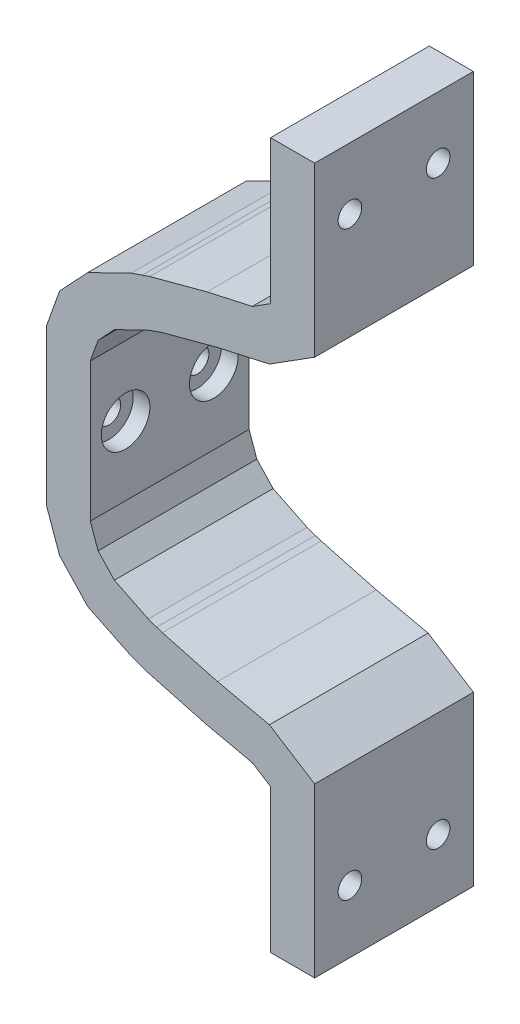
SolidWorks part; units mm, degrees
ref_plane "Front Plane" through (0, 0, 0) normal (0, 0, 1) x (1, 0, 0)
ref_plane "Top Plane" through (0, 0, 0) normal (0, 1, 0) x (1, 0, 0)
ref_plane "Right Plane" through (0, 0, 0) normal (1, 0, 0) x (0, 0, -1)
sketch "Model" plane through (0, 0, 0) normal (0, 0, 1) x (1, 0, 0)
  line L0 (-31.5615, 5.719) -> (-31.5592, -16.7565)
  line L35 (-15.7136, 12.9115) -> (-14.8809, 13.188)
  line L36 (-14.8809, 13.188) -> (-6.9454, 15.3129)
  line L37 (-6.9454, 15.3129) -> (0.5162, 16.9685)
  line L38 (0.5162, 16.9685) -> (7.0365, 21.0824)
  line L53 (0.5162, -28.0048) -> (7.0365, -32.1186)
  line L54 (-6.9454, -26.3491) -> (0.5162, -28.0048)
  line L55 (-14.8809, -24.2242) -> (-6.9454, -26.3491)
  line L56 (-15.7136, -23.9477) -> (-14.8809, -24.2242)
  line L57 (-16.9096, -23.527) -> (-15.7136, -23.9477)
  line L58 (-21.8042, -21.1418) -> (-16.9096, -23.527)
  line L59 (-24.1425, -18.6446) -> (-21.8042, -21.1418)
  line L60 (-25.2646, -15.5017) -> (-24.1425, -18.6446)
  line L65 (-25.2667, 4.4655) -> (-24.1471, 7.6035)
  line L66 (-24.1471, 7.6035) -> (-21.8042, 10.1055)
  line L67 (-21.8042, 10.1055) -> (-16.9096, 12.4907)
  line L68 (-16.9096, 12.4907) -> (-15.7136, 12.9115)
  line L71 (0.6865, -35.6205) -> (0.6865, -56.3181)
  line L72 (-17.768, 18.9202) -> (-16.7043, 19.2734)
  line L73 (-16.7043, 19.2734) -> (-8.4551, 21.4823)
  line L74 (-8.4551, 21.4823) -> (-1.9379, 22.9284)
  line L75 (-1.9379, 22.9284) -> (0.6865, 24.5842)
  line L77 (52.7242, -5.5181) -> (1077.4342, -5.5181) construction
  line L78 (-1.9379, -33.9647) -> (0.6865, -35.6205)
  line L79 (-8.4551, -32.5186) -> (-1.9379, -33.9647)
  line L80 (-16.7043, -30.3097) -> (-8.4551, -32.5186)
  line L81 (-17.768, -29.9565) -> (-16.7043, -30.3097)
  line L82 (-19.3623, -29.3956) -> (-17.768, -29.9565)
  line L83 (-25.6388, -26.337) -> (-19.3623, -29.3956)
  line L84 (-29.6793, -22.0221) -> (-25.6388, -26.337)
  line L85 (-31.5592, -16.7565) -> (-29.6793, -22.0221)
  line L90 (-31.5615, 5.719) -> (-29.6843, 10.9804)
  line L91 (-29.6843, 10.9804) -> (-25.6388, 15.3007)
  line L92 (-25.6388, 15.3007) -> (-19.3623, 18.3593)
  line L93 (-19.3623, 18.3593) -> (-17.768, 18.9202)
  line L95 (7.0365, 45.2819) -> (0.6865, 45.2819)
  line L106 (7.0365, -56.3181) -> (0.6865, -56.3181)
  line L107 (0.6865, 45.2819) -> (0.6865, 24.5842)
  line L108 (7.0365, 21.0824) -> (7.0365, 45.2819)
  line L109 (7.0365, -32.1186) -> (7.0365, -56.3181)
  line L111 (-25.2667, 4.4655) -> (-25.2646, -15.5017)
  dimension "D1" = 0.5162
  dimension "D2" = 0.6865
  dimension "D3" = 7.0365
  dimension "D4" = 1.9379
  dimension "D5" = 6.9454
  dimension "D6" = 8.4551
  dimension "D7" = 14.8809
  dimension "D8" = 15.7136
  dimension "D9" = 16.7043
  dimension "D10" = 16.9096
  dimension "D11" = 17.768
  dimension "D12" = 19.3623
  dimension "D13" = 21.8042
  dimension "D14" = 24.1425
  dimension "D15" = 24.1471
  dimension "D16" = 25.2646
  dimension "D17" = 25.2667
  dimension "D18" = 25.6388
  dimension "D19" = 29.6793
  dimension "D20" = 29.6843
  dimension "D21" = 31.5592
  dimension "D22" = 31.5615
  dimension "D24" = 4.4655
  dimension "D25" = 5.719
  dimension "D26" = 7.6035
  dimension "D27" = 10.1055
  dimension "D28" = 10.9804
  dimension "D29" = 12.4907
  dimension "D30" = 12.9115
  dimension "D31" = 13.188
  dimension "D32" = 15.3007
  dimension "D33" = 15.3129
  dimension "D34" = 16.9685
  dimension "D35" = 18.3593
  dimension "D36" = 18.9202
  dimension "D37" = 19.2734
  dimension "D38" = 21.0824
  dimension "D39" = 21.4823
  dimension "D40" = 22.9284
  dimension "D41" = 24.5842
  dimension "D42" = 45.2819
  dimension "D45" = 15.5017
  dimension "D46" = 16.7565
  dimension "D47" = 18.6446
  dimension "D48" = 21.1418
  dimension "D49" = 22.0221
extrude "Boss-Extrude1" add sketch "Model" along normal blind 22.86 contours L74 L75 L107 L95 L108 L38 L37 L36 L35 L68 L67 L66 L65 L111 L60 L59 L58 L57 L56 L55 L54 L53 L109 L106 L71 L78 L79 L80 L81 L82 L83 L84 L85 L0 L90 L91 L92 L93 L72 L73
hole_wizard "M3 Clearance Hole1" positions "Sketch1" profile "Sketch2" hole size "M3" standard "ANSI Metric" end condition through all
sketch "Sketch1" plane through (0.6865, 0, 0) normal (-1, 0, 0) x (0, 0, 1)
  line L0 (0, 45.2819) -> (0, 24.5842) construction
  line L1 (22.86, 45.2819) -> (0, 45.2819) construction
  line L2 (0, -35.6205) -> (0, -56.3181) construction
  line L4 (22.86, -56.3181) -> (0, -56.3181) construction
  point P0 (5.08, 36.3919)
  point P2 (17.78, 36.3919)
  point P4 (5.08, -47.3087)
  point P6 (17.78, -47.3087)
  point P29 (0, 0)
  dimension "D1" = 12.7
  dimension "D2" = 5.08
  dimension "D3" = 8.89
  dimension "D4" = 8.89
  dimension "D5" = 12.7
  dimension "D6" = 5.08
  dimension "D7" = 9.0094
  dimension "D8" = 9.0094
sketch "Sketch2" plane through (0.6865, 36.3919, 5.08) normal (0, 1, 0) x (0, 0, 1)
  line L0 (0, 0) -> (0, 6.35)
  line L1 (0, 6.35) -> (1.7, 6.35)
  line L2 (1.7, 6.35) -> (1.7, 0)
  line L5 (1.7, 0) -> (0, 0)
  line L11 (0, -6.35) -> (0, 107.95) construction
  dimension "Thru Hole Dia." = 3.4
  dimension "Thru Hole Depth" = 6.35
hole_wizard "CBORE for M3 Pan Head Machine Screw1" positions "Sketch3" profile "Sketch4" counterbore size "M3" standard "ANSI Metric" end condition through all
sketch "Sketch3" plane through (-25.2662, -0.0026, 0) normal (1, 0.0001, 0) x (0, 0, -1)
  line L0 (-22.86, 4.4682) -> (-22.86, -15.4991) construction
  line L1 (-22.86, 4.4682) -> (0, 4.4682) construction
  point P0 (-5.08, -5.5648)
  point P2 (-17.78, -5.5648)
  dimension "D1" = 5.08
  dimension "D2" = 12.7
  dimension "D3" = 10.033
sketch "Sketch4" plane through (-25.2656, -5.5675, 5.08) normal (0, 0, 1) x (-0.0001, 1, 0)
  line L0 (0, 0) -> (0, 6.3012)
  line L1 (0, 6.3012) -> (1.7, 6.3012)
  line L3 (1.7, 6.3012) -> (1.7, 2.4)
  line L4 (1.7, 2.4) -> (3.5, 2.4)
  line L5 (3.5, 2.4) -> (3.5, 0)
  line L7 (3.5, 0) -> (0, 0)
  line L11 (0, -6.35) -> (0, 107.95) construction
  dimension "Thru Hole Dia." = 3.4
  dimension "Thru Hole Depth" = 6.3012
  dimension "C'Bore Dia." = 7
  dimension "C'Bore Depth" = 2.4
sketch "Sketch5" plane through (0.6865, 0, 0) normal (-1, 0, 0) x (0, 0, 1)
  line L0 (0, -35.6205) -> (0, -56.3181) construction
  line L1 (17.78, -43.6426) -> (14.605, -45.4756)
  line L2 (14.605, -45.4756) -> (14.605, -49.1418)
  line L3 (14.605, -49.1418) -> (17.78, -50.9749)
  line L4 (17.78, -50.9749) -> (20.955, -49.1418)
  line L5 (20.955, -49.1418) -> (20.955, -45.4756)
  line L6 (20.955, -45.4756) -> (17.78, -43.6426)
  line L7 (5.08, -43.6426) -> (1.905, -45.4756)
  line L8 (1.905, -45.4756) -> (1.905, -49.1418)
  line L9 (1.905, -49.1418) -> (5.08, -50.9749)
  line L10 (5.08, -50.9749) -> (8.255, -49.1418)
  line L11 (8.255, -49.1418) -> (8.255, -45.4756)
  line L12 (8.255, -45.4756) -> (5.08, -43.6426)
  line L13 (17.78, 40.058) -> (14.605, 38.225)
  line L14 (14.605, 38.225) -> (14.605, 34.5588)
  line L15 (14.605, 34.5588) -> (17.78, 32.7257)
  line L16 (17.78, 32.7257) -> (20.955, 34.5588)
  line L17 (20.955, 34.5588) -> (20.955, 38.225)
  line L18 (20.955, 38.225) -> (17.78, 40.058)
  line L19 (5.08, 40.058) -> (1.905, 38.225)
  line L20 (1.905, 38.225) -> (1.905, 34.5588)
  line L21 (1.905, 34.5588) -> (5.08, 32.7257)
  line L22 (5.08, 32.7257) -> (8.255, 34.5588)
  line L23 (8.255, 34.5588) -> (8.255, 38.225)
  line L24 (8.255, 38.225) -> (5.08, 40.058)
  line L25 (0, 45.2819) -> (0, 24.5842) construction
  circle A0 centre (17.78, -47.3087) radius 3.175 construction
  circle A1 centre (5.08, -47.3087) radius 3.175 construction
  circle A2 centre (17.78, 36.3919) radius 3.175 construction
  circle A3 centre (5.08, 36.3919) radius 3.175 construction
  point P40 (0, 0)
extrude "Cut-Extrude1" cut sketch "Sketch5" against normal blind 2.54
